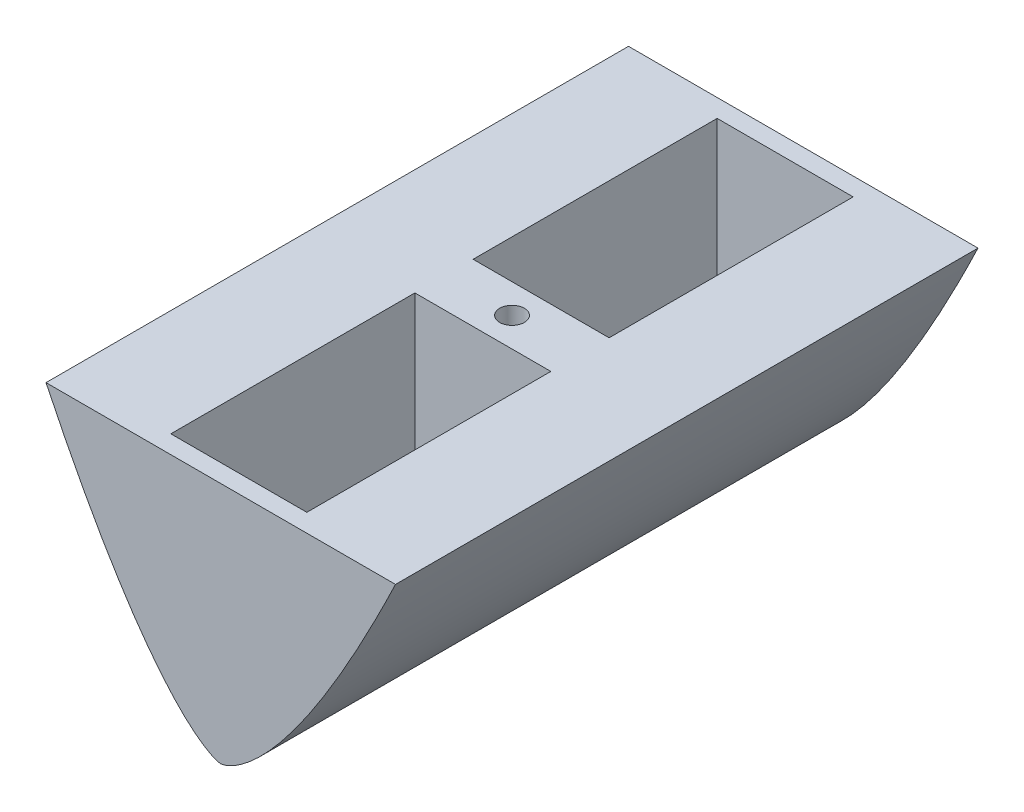
SolidWorks part; units mm, degrees
ref_plane "Front" through (0, 0, 0) normal (0, 0, 1) x (1, 0, 0)
ref_plane "Top" through (0, 0, 0) normal (0, 1, 0) x (1, 0, 0)
ref_plane "Right" through (0, 0, 0) normal (1, 0, 0) x (0, 0, -1)
sketch "Sketch1" plane through (0, 0, 0) normal (0, 0, 1) x (1, 0, 0)
  line L0 (-90, 0) -> (90, 0)
  spline S0 degree 4 poles (0, -125) (0.0405, -125) (0.1327, -124.9944) (0.3419, -124.9736) (0.7192, -124.9167) (1.2894, -124.7957) (2.1113, -124.565) (3.1882, -124.1854) (4.5534, -123.6021) (6.24, -122.7495) (8.3035, -121.5375) (10.7243, -119.9063) (13.7092, -117.6331) (17.1253, -114.7) (20.8249, -111.1645) (25.6392, -106.1097) (30.2222, -100.7811) (34.5982, -95.2835) (38.7797, -89.6846) (42.0337, -85.1392) (45.9986, -79.3851) (50.6077, -72.3799) (55.0551, -65.2706) (59.3647, -58.0777) (62.8735, -52.0349) (65.6341, -47.1745) (68.3516, -42.289) (71.0277, -37.3821) (73.6663, -32.4526) (76.267, -27.507) (78.515, -23.1588) (80.4175, -19.4295) (81.9961, -16.3021) (83.2401, -13.8196) (84.4993, -11.2862) (85.7105, -8.8337) (86.9855, -6.23) (88.1249, -3.8908) (89.6506, -0.7311) (90.7655, 1.5945) (92.6806, 5.6147) (94.0542, 8.5406) (95.5196, 11.6646) (96.2013, 13.1419) (96.6746, 14.1591) knots 0 0 0 0 0 0.001034 0.002068 0.004832 0.008889 0.014522 0.021877 0.031298 0.043316 0.058339 0.077369 0.098985 0.130325 0.16275 0.196051 0.260901 0.293325 0.32575 0.358175 0.3906 0.455449 0.520299 0.552723 0.585148 0.617573 0.649998 0.682423 0.714847 0.747272 0.779697 0.795909 0.812122 0.828334 0.844546 0.860759 0.876971 0.893184 0.909396 0.932047 0.954698 0.977349 1 1 1 1 1 construction
  spline S1 degree 4 poles (0, -125) (0.0405, -125) (0.1327, -124.9944) (0.3419, -124.9736) (0.7192, -124.9167) (1.2894, -124.7957) (2.1113, -124.565) (3.1882, -124.1854) (4.5534, -123.6021) (6.24, -122.7495) (8.3035, -121.5375) (10.7243, -119.9063) (13.7092, -117.6331) (17.1253, -114.7) (20.8249, -111.1645) (25.6392, -106.1097) (30.2222, -100.7811) (34.5982, -95.2835) (38.7797, -89.6846) (42.0337, -85.1392) (45.9986, -79.3851) (50.6077, -72.3799) (55.0551, -65.2706) (59.3647, -58.0777) (62.8735, -52.0349) (65.6341, -47.1745) (68.3516, -42.289) (71.0277, -37.3821) (73.6663, -32.4526) (76.267, -27.507) (78.515, -23.1588) (80.4175, -19.4295) (81.9961, -16.3021) (83.2401, -13.8196) (84.4993, -11.2862) (85.7105, -8.8337) (86.9855, -6.23) (88.1249, -3.8908) (89.1658, -1.7351) (89.725, -0.5729) (90, 0) knots 0 0 0 0 0 0.001034 0.002068 0.004832 0.008889 0.014522 0.021877 0.031298 0.043316 0.058339 0.077369 0.098985 0.130325 0.16275 0.196051 0.260901 0.293325 0.32575 0.358175 0.3906 0.455449 0.520299 0.552723 0.585148 0.617573 0.649998 0.682423 0.714847 0.747272 0.779697 0.795909 0.812122 0.828334 0.844546 0.860759 0.876971 0.893184 0.909396 0.909396 0.909396 0.909396 0.909396
  spline S2 degree 4 poles (-96.6747, 14.1592) (-96.201, 13.1414) (-95.5202, 11.6656) (-94.0535, 8.539) (-92.6815, 5.6165) (-90.7695, 1.6028) (-89.6608, -0.7099) (-88.1523, -3.8342) (-87.0256, -6.1478) (-85.7702, -8.7121) (-84.575, -11.1331) (-83.3335, -13.6323) (-82.108, -16.0794) (-80.8613, -18.5513) (-79.6147, -21.0032) (-78.0419, -24.0731) (-76.1411, -27.7433) (-73.8976, -32.0158) (-71.2994, -36.8782) (-68.6635, -41.7214) (-65.3196, -47.7478) (-61.9058, -53.7355) (-58.4154, -59.6786) (-54.1245, -66.7492) (-50.4569, -72.5848) (-46.6862, -78.3546) (-42.0197, -85.1832) (-37.1972, -91.9035) (-31.9659, -98.6944) (-26.424, -105.2353) (-21.5051, -110.4838) (-17.6258, -114.2413) (-14.1803, -117.2485) (-11.1235, -119.6187) (-8.6356, -121.3268) (-6.5087, -122.6017) (-4.7682, -123.5012) (-3.3619, -124.1173) (-2.2393, -124.5242) (-1.382, -124.7727) (-0.7562, -124.911) (-0.3473, -124.9739) (-0.1234, -124.9953) (-0.0205, -125) (0, -125) knots 0 0 0 0 0 0.022651 0.045302 0.067953 0.090604 0.106595 0.122587 0.138578 0.154569 0.17056 0.186552 0.202543 0.218534 0.234526 0.250517 0.282499 0.314482 0.346465 0.378447 0.41043 0.474395 0.506377 0.53836 0.602325 0.634308 0.66629 0.730255 0.794221 0.833134 0.865117 0.897099 0.919479 0.939186 0.954818 0.967077 0.976979 0.984613 0.990417 0.994764 0.997672 0.999477 1 1 1 1 1 construction
  spline S3 degree 4 poles (-90, 0) (-89.7288, -0.565) (-89.177, -1.7119) (-88.1523, -3.8342) (-87.0256, -6.1478) (-85.7702, -8.7121) (-84.575, -11.1331) (-83.3335, -13.6323) (-82.108, -16.0794) (-80.8613, -18.5513) (-79.6147, -21.0032) (-78.0419, -24.0731) (-76.1411, -27.7433) (-73.8976, -32.0158) (-71.2994, -36.8782) (-68.6635, -41.7214) (-65.3196, -47.7478) (-61.9058, -53.7355) (-58.4154, -59.6786) (-54.1245, -66.7492) (-50.4569, -72.5848) (-46.6862, -78.3546) (-42.0197, -85.1832) (-37.1972, -91.9035) (-31.9659, -98.6944) (-26.424, -105.2353) (-21.5051, -110.4838) (-17.6258, -114.2413) (-14.1803, -117.2485) (-11.1235, -119.6187) (-8.6356, -121.3268) (-6.5087, -122.6017) (-4.7682, -123.5012) (-3.3619, -124.1173) (-2.2393, -124.5242) (-1.382, -124.7727) (-0.7562, -124.911) (-0.3473, -124.9739) (-0.1234, -124.9953) (-0.0205, -125) (0, -125) knots 0.090604 0.090604 0.090604 0.090604 0.090604 0.106595 0.122587 0.138578 0.154569 0.17056 0.186552 0.202543 0.218534 0.234526 0.250517 0.282499 0.314482 0.346465 0.378447 0.41043 0.474395 0.506377 0.53836 0.602325 0.634308 0.66629 0.730255 0.794221 0.833134 0.865117 0.897099 0.919479 0.939186 0.954818 0.967077 0.976979 0.984613 0.990417 0.994764 0.997672 0.999477 1 1 1 1 1
extrude "Boss-Extrude1" add sketch "Sketch1" against normal mid plane 300
sketch "Sketch2" plane through (0, 0, 0) normal (0, 1, 0) x (1, 0, 0)
  line L0 (0, 0) -> (0, -150) construction
  line L1 (90, -150) -> (-90, -150) construction
  line L2 (0, 0) -> (0, 150) construction
  line L3 (90, 150) -> (-90, 150) construction
  line L4 (-90, 0) -> (90, 0) construction
  line L5 (35.02, 140.682) -> (-35.02, 140.682)
  line L6 (35.02, 140.682) -> (35.02, 15)
  line L7 (35.02, 15) -> (-35.02, 15)
  line L8 (-35.02, 140.682) -> (-35.02, 15)
  line L9 (35.02, 140.682) -> (-35.02, 15) construction
  line L10 (35.02, 15) -> (-35.02, 140.682) construction
  line L11 (-90, 150) -> (-90, -150) construction
  line L12 (90, 150) -> (90, -150) construction
  line L13 (35.02, -140.682) -> (-35.02, -140.682)
  line L14 (-35.02, -140.682) -> (-35.02, -15)
  line L15 (35.02, -15) -> (-35.02, -15)
  line L16 (35.02, -140.682) -> (35.02, -15)
  point P9 (0, 77.841)
  dimension "D2" = 125.682
  dimension "D3" = 15
  dimension "D4" = 70.04
extrude "Cut-Extrude1" cut sketch "Sketch2" against normal blind 92.52
sketch "Sketch4" plane through (0, 0, 0) normal (0, 1, 0) x (1, 0, 0)
  circle A0 centre (0, 0) radius 6.35
  dimension "D1" = 12.7
extrude "Cut-Extrude2" cut sketch "Sketch4" against normal through all
sketch "Sketch5" plane through (0, 0, -150) normal (0, 0, -1) x (-1, 0, 0)
  line L0 (0, 0) -> (0, -125) construction
  line L1 (-90, 0) -> (90, 0) construction
ref_plane "Plane1" through (0, -92.52, 0) normal (0, 1, 0) x (1, 0, 0)
ref_plane "Plane2" through (0, -41.72, 0) normal (0, 1, 0) x (1, 0, 0)
split "Split2" bodies to split 103
